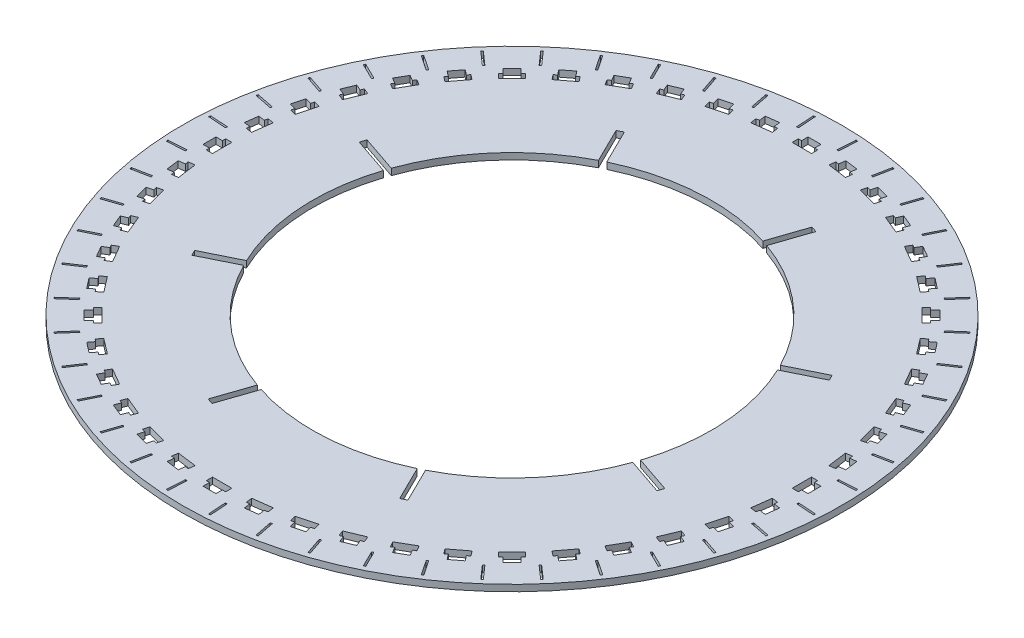
SolidWorks part; units mm, degrees
ref_plane "前视基准面" through (0, 0, 0) normal (0, 0, 1) x (1, 0, 0)
ref_plane "上视基准面" through (0, 0, 0) normal (0, 1, 0) x (1, 0, 0)
ref_plane "右视基准面" through (0, 0, 0) normal (1, 0, 0) x (0, 0, -1)
sketch "草图1" plane through (0, 0, 0) normal (0, 1, 0) x (1, 0, 0)
  circle A0 centre (0, 0) radius 254.62
  circle A1 centre (0, 0) radius 154.62
  dimension "D1" = 509.24
  dimension "D2" = 100
extrude "凸台-拉伸1" add sketch "草图1" along normal blind 5
sketch "草图2" plane through (0, 5, 0) normal (0, 1, 0) x (1, 0, 0)
  line L0 (0, 0) -> (0, -254.62) construction
  line L1 (-121.5945, -254.62) -> (118.2632, -254.62) construction
  line L3 (-5, -234.62) -> (5, -234.62)
  line L4 (-5, -234.62) -> (-5, -229.62)
  line L5 (-5, -229.62) -> (5, -229.62)
  line L6 (5, -234.62) -> (5, -229.62)
  line L7 (-5, -234.62) -> (5, -229.62) construction
  line L8 (-5, -229.62) -> (5, -234.62) construction
  line L9 (-7.5, -224.82) -> (7.5, -224.82)
  line L10 (-7.5, -224.82) -> (-7.5, -229.62)
  line L11 (-7.5, -229.62) -> (7.5, -229.62)
  line L12 (7.5, -224.82) -> (7.5, -229.62)
  line L13 (-7.5, -224.82) -> (7.5, -229.62) construction
  line L14 (-7.5, -229.62) -> (7.5, -224.82) construction
  circle A0 centre (0, 0) radius 254.62 construction
  point P8 (0, -232.12)
  point P13 (0, -227.22)
  dimension "D1" = 10
  dimension "D2" = 5
  dimension "D3" = 20
  dimension "D4" = 15
  dimension "D5" = 4.8
extrude "切除-拉伸1" cut sketch "草图2" against normal through all contours L12 L9 L10 L11 L5 | L3 L6 L5 L4
pattern_circular "阵列(圆周)1" count 48 every 7.5 about axis through (0, 0, 0) along (0, 1, 0) of "切除-拉伸1"
sketch "草图3" plane through (0, 5, 0) normal (0, 1, 0) x (1, 0, 0)
  line L0 (0, -272.4222) -> (0, 0) construction
  line L1 (0, 0) -> (36.5803, -277.8552) construction
  line L2 (0, 0) -> (16.2369, -247.7265) construction
  line L3 (14.287, -217.9772) -> (0, -217.9772) construction
  line L4 (14.287, -217.9772) -> (28.4517, -216.1123) construction
  line L5 (21.9091, -223.8756) -> (36.7807, -221.9177) construction
  line L6 (3.172, -254.9584) -> (27.7261, -253.3491) construction
  line L7 (15.7582, -251.127) -> (14.8426, -237.157)
  line L8 (15.7582, -251.127) -> (17.1552, -251.0355)
  line L9 (14.8426, -237.157) -> (16.2396, -237.0655)
  line L10 (17.1552, -251.0355) -> (16.2396, -237.0655)
  line L11 (15.7582, -251.127) -> (16.2396, -237.0655) construction
  line L12 (14.8426, -237.157) -> (17.1552, -251.0355) construction
  circle A0 centre (0, 0) radius 254.62 construction
  point P15 (15.9989, -244.0962)
  dimension "D1" = 1.4
  dimension "D2" = 14
  dimension "D3" = 10
extrude "切除-拉伸2" cut sketch "草图3" against normal up to next (5 mm away)
pattern_circular "阵列(圆周)2" count 48 every 7.5 about axis through (0, 0, 0) along (0, 1, 0) of "切除-拉伸2"
sketch "草图4" plane through (0, 5, 0) normal (0, 1, 0) x (1, 0, 0)
  circle A0 centre (0, 0) radius 254.62
  circle A1 centre (0, 0) radius 255.62
  circle A2 centre (0, 0) radius 254.62 construction
  dimension "D1" = 1
extrude "凸台-拉伸2" add sketch "草图4" against normal blind 5
sketch "草图6" plane through (0, 5, 0) normal (0, 1, 0) x (1, 0, 0)
  line L0 (0, 0) -> (205.0681, 101.1284) construction
  line L1 (209.2711, 94.8009) -> (0, 0) construction
  line L2 (202.6068, 108.3148) -> (0, 0) construction
  line L3 (83.3454, 41.1014) -> (84.6029, 38.3256) construction
  line L4 (83.3454, 41.1014) -> (81.9087, 43.7889) construction
  line L5 (112.8298, 52.9655) -> (166.6421, 79.5028)
  line L6 (112.8298, 52.9655) -> (110.7068, 57.2705)
  line L7 (166.6421, 79.5028) -> (164.5192, 83.8078)
  line L8 (110.7068, 57.2705) -> (164.5192, 83.8078)
  line L9 (112.8298, 52.9655) -> (164.5192, 83.8078) construction
  line L10 (166.6421, 79.5028) -> (110.7068, 57.2705) construction
  circle A0 centre (0, 0) radius 154.62 construction
  point P9 (0, 0)
  point P11 (138.6745, 68.3867)
  point P14 (144.2115, 55.7709)
  point P15 (0, 0)
  dimension "D1" = 4.8
  dimension "D2" = 30
extrude "切除-拉伸3" cut sketch "草图6" against normal up to next (5 mm away)
pattern_circular "阵列(圆周)3" count 8 every 45 about axis through (0, 0, 0) along (0, 1, 0) of "切除-拉伸3"
